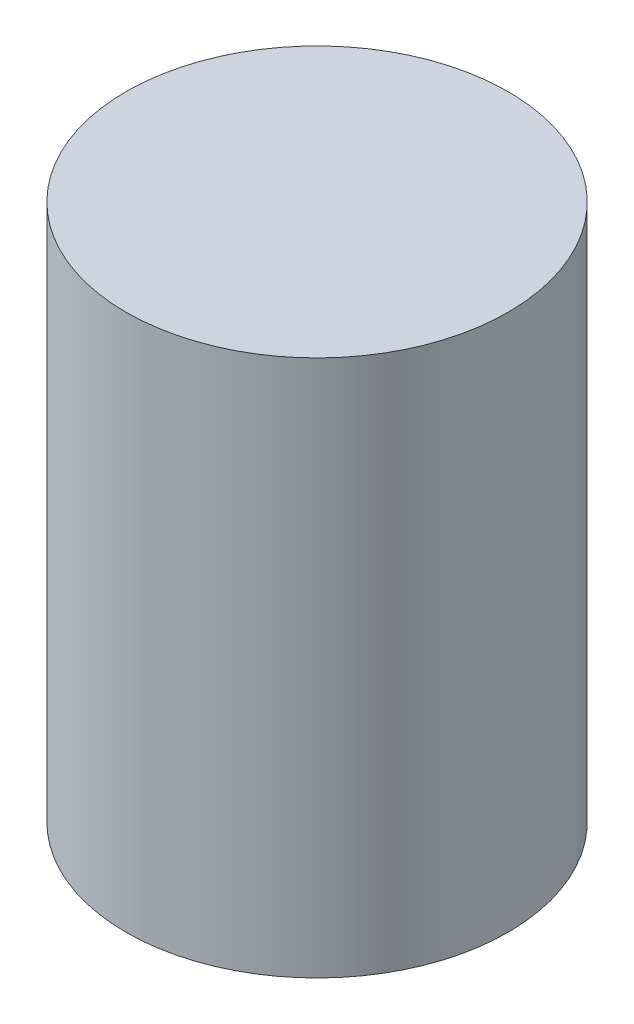
SolidWorks part; units mm, degrees
ref_plane "Front Plane" through (0, 0, 0) normal (0, 0, 1) x (1, 0, 0)
ref_plane "Top Plane" through (0, 0, 0) normal (0, 1, 0) x (1, 0, 0)
ref_plane "Right Plane" through (0, 0, 0) normal (1, 0, 0) x (0, 0, -1)
sketch "Sketch1" plane through (0, 0, 0) normal (0, 1, 0) x (1, 0, 0)
  line L0 (0, 0) -> (-131.3975, -49.2086) construction
  circle A0 centre (0, -45.445) radius 1.925
extrude "Boss-Extrude1" add sketch "Sketch1" along normal blind 5.4102
